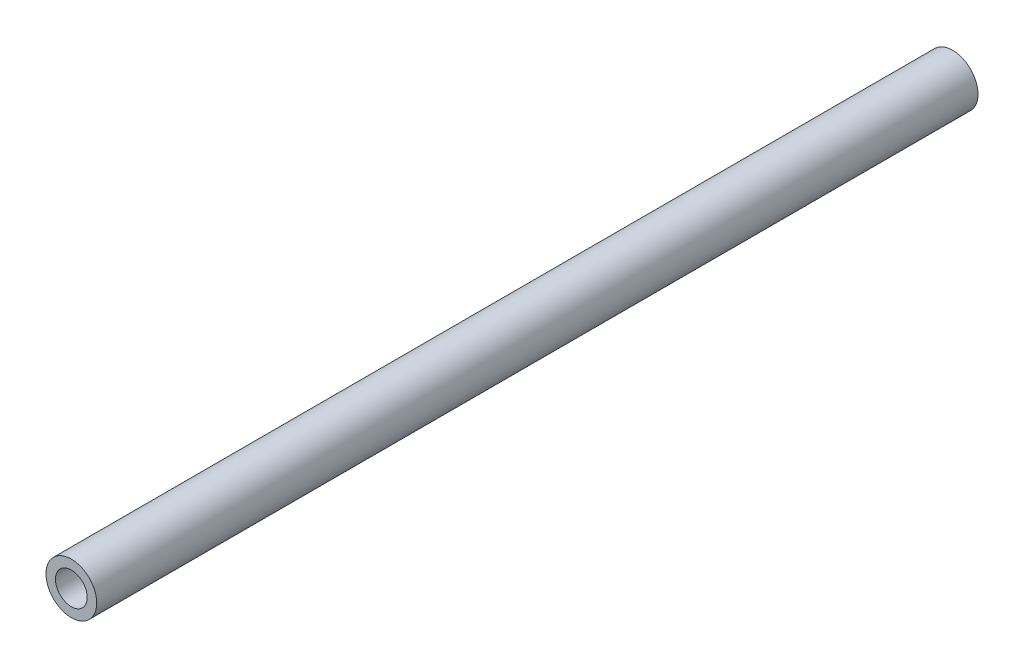
SolidWorks part; units mm, degrees
material "AISI 304"
ref_plane "Front Plane" through (0, 0, 0) normal (0, 0, 1) x (1, 0, 0)
ref_plane "Top Plane" through (0, 0, 0) normal (0, 1, 0) x (1, 0, 0)
ref_plane "Right Plane" through (0, 0, 0) normal (1, 0, 0) x (0, 0, -1)
sketch "Sketch1" plane through (0, 0, 0) normal (0, 0, 1) x (1, 0, 0)
  circle A0 centre (0, 0) radius 8.55
  circle A1 centre (0, 0) radius 5.35
  dimension "D1" = 10.7
  dimension "D2" = 17.1
extrude "Boss-Extrude1" add sketch "Sketch1" against normal blind 296.85
